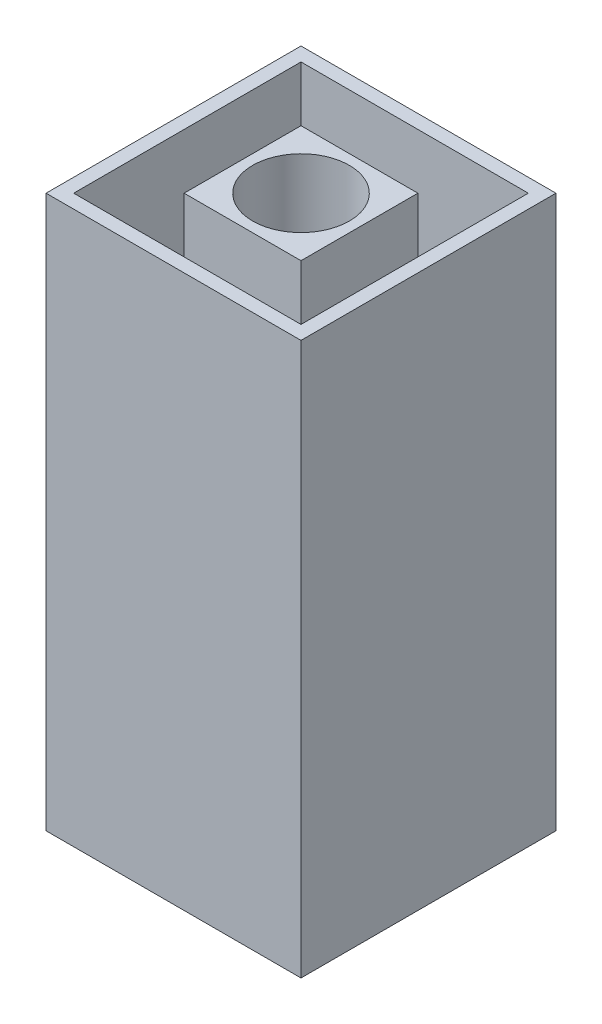
SolidWorks part; units mm, degrees
material "Plain Carbon Steel"
ref_plane "Front" through (0, 0, 0) normal (0, 0, 1) x (1, 0, 0)
ref_plane "Top" through (0, 0, 0) normal (0, 1, 0) x (1, 0, 0)
ref_plane "Right" through (0, 0, 0) normal (1, 0, 0) x (0, 0, -1)
sketch "Sketch1" plane through (0, 0, 0) normal (0, 1, 0) x (1, 0, 0)
  line L1 (-1.385, 1.385) -> (1.385, 1.385)
  line L2 (-1.385, 1.385) -> (-1.385, -1.385)
  line L3 (-1.385, -1.385) -> (1.385, -1.385)
  line L4 (1.385, 1.385) -> (1.385, -1.385)
  line L5 (-1.385, 1.385) -> (1.385, -1.385) construction
  line L6 (-1.385, -1.385) -> (1.385, 1.385) construction
  point P0 (0, 0)
  dimension "D1" = 2.77
  dimension "D2" = 2.77
extrude "Boss-Extrude1" add sketch "Sketch1" along normal blind 6
sketch "Sketch2" plane through (0, 6, 0) normal (0, 1, 0) x (1, 0, 0)
  circle A0 centre (0, 0) radius 0.525
  dimension "D1" = 1.05
extrude "Cut-Extrude1" cut sketch "Sketch2" against normal through all
sketch "Sketch3" plane through (0, 6, 0) normal (0, 1, 0) x (1, 0, 0)
  line L0 (-1.385, 1.385) -> (-1.385, -1.385) construction
  line L1 (-1.235, 1.235) -> (1.235, 1.235)
  line L2 (-1.235, 1.235) -> (-1.235, -1.235)
  line L3 (-1.235, -1.235) -> (1.235, -1.235)
  line L4 (1.235, 1.235) -> (1.235, -1.235)
  line L5 (-0.635, 0.635) -> (0.635, 0.635)
  line L6 (-0.635, 0.635) -> (-0.635, -0.635)
  line L7 (-0.635, -0.635) -> (0.635, -0.635)
  line L8 (0.635, 0.635) -> (0.635, -0.635)
  line L9 (-1.385, -1.385) -> (1.385, -1.385) construction
  line L10 (1.385, 1.385) -> (-1.385, 1.385) construction
  line L11 (1.385, -1.385) -> (1.385, 1.385) construction
  dimension "D1" = 0.6
  dimension "D2" = 0.6
  dimension "D3" = 0.6
  dimension "D4" = 0.6
  dimension "D5" = 0.15
  dimension "D6" = 0.15
  dimension "D7" = 0.15
  dimension "D8" = 0.15
extrude "Cut-Extrude2" cut sketch "Sketch3" against normal blind 10
